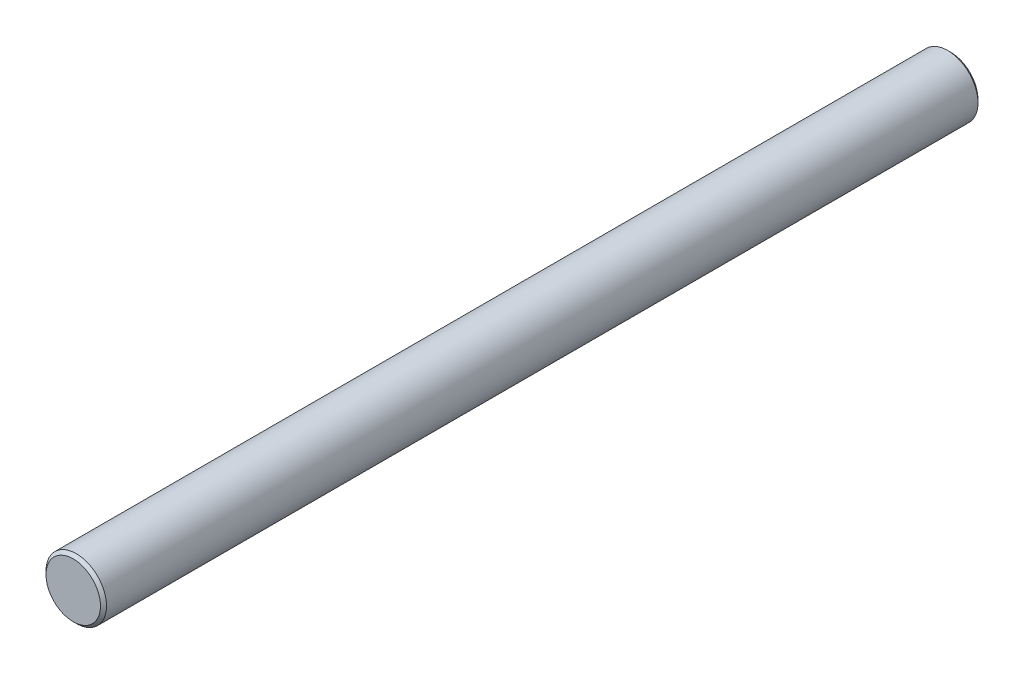
SolidWorks part; units mm, degrees
ref_plane "Front Plane" through (0, 0, 0) normal (0, 0, 1) x (1, 0, 0)
ref_plane "Top Plane" through (0, 0, 0) normal (0, 1, 0) x (1, 0, 0)
ref_plane "Right Plane" through (0, 0, 0) normal (1, 0, 0) x (0, 0, -1)
sketch "Sketch1" plane through (0, 0, 0) normal (0, 0, 1) x (1, 0, 0)
  circle A0 centre (0, 0) radius 5
  dimension "D1" = 10
extrude "Boss-Extrude1" add sketch "Sketch1" along normal blind 145
sketch "Sketch2" plane through (0, 0, 0) normal (0, 0, -1) x (-1, 0, 0)
  line L0 (4, 3) -> (4, -3)
  circle A0 centre (0, 0) radius 5 construction
  arc A1 (4, -3) -> (4, 3) centre (0, 0) ccw
  point P8 (0, 0)
  dimension "D1" = 4
extrude "Cut-Extrude1" cut sketch "Sketch2" against normal blind 8
chamfer "Chamfer1" distance 0.5 angle 45 2 edges at (5, 0, 0) (5, 0, 145)
